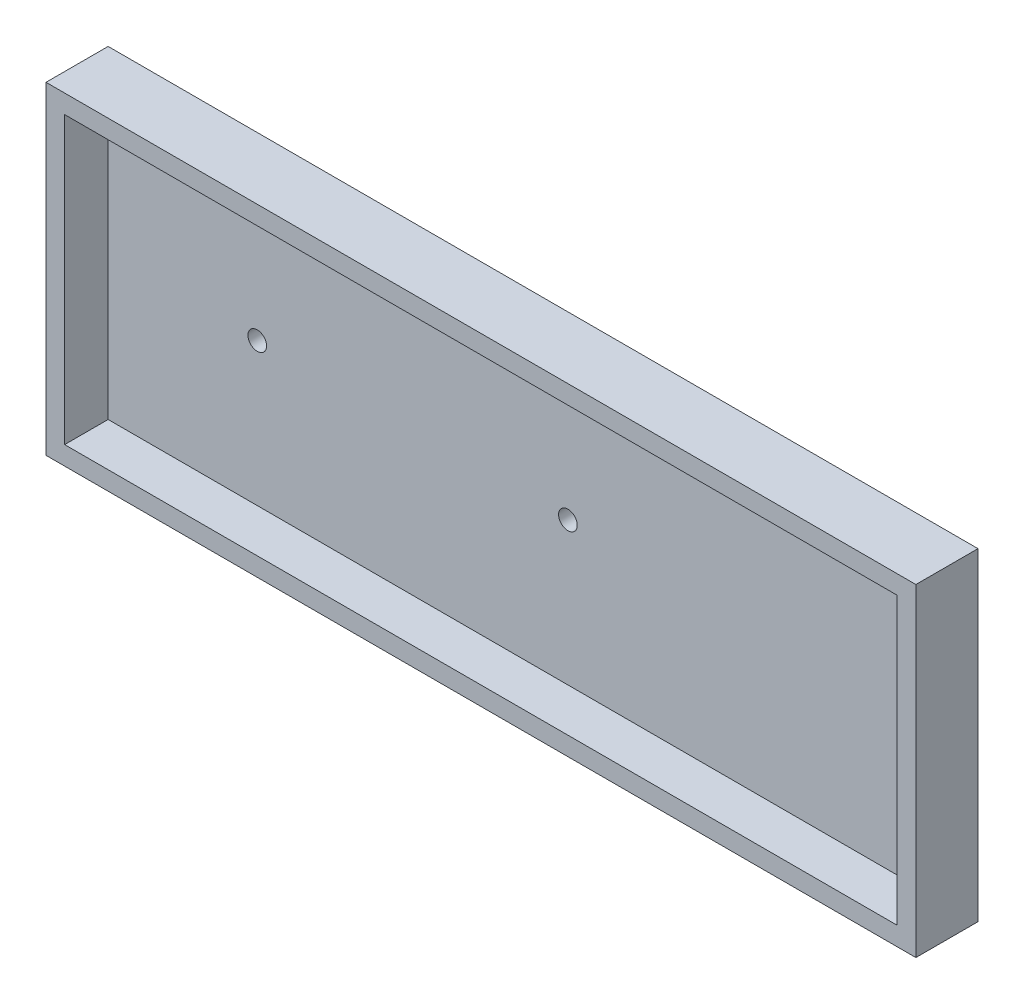
SolidWorks part; units mm, degrees
ref_plane "Front Plane" through (0, 0, 0) normal (0, 0, 1) x (1, 0, 0)
ref_plane "Top Plane" through (0, 0, 0) normal (0, 1, 0) x (1, 0, 0)
ref_plane "Right Plane" through (0, 0, 0) normal (1, 0, 0) x (0, 0, -1)
sketch "Sketch1" plane through (0, 0, 0) normal (0, 0, 1) x (1, 0, 0)
  line L1 (-35, -13) -> (35, -13)
  line L2 (-35, -13) -> (-35, 13)
  line L3 (-35, 13) -> (35, 13)
  line L4 (35, -13) -> (35, 13)
  line L5 (-35, -13) -> (35, 13) construction
  line L6 (-35, 13) -> (35, -13) construction
  point P0 (0, 0)
  dimension "D1" = 70
  dimension "D2" = 26
extrude "Boss-Extrude1" add sketch "Sketch1" along normal blind 5
shell "Shell1" thickness 1.5
sketch "Sketch2" plane through (0, 0, 1.5) normal (0, 0, 1) x (1, 0, 0)
  line L0 (-1000, 0) -> (49000, 0) construction
  line L1 (-33.5, 11.5) -> (-33.5, -11.5) construction
  circle A0 centre (-21.5, 0) radius 0.75
  circle A1 centre (3.5, 0) radius 0.75
  dimension "D3" = 1.5
  dimension "D4" = 1.5
  dimension "D1" = 12
  dimension "D2" = 25
extrude "Cut-Extrude1" cut sketch "Sketch2" against normal through all
